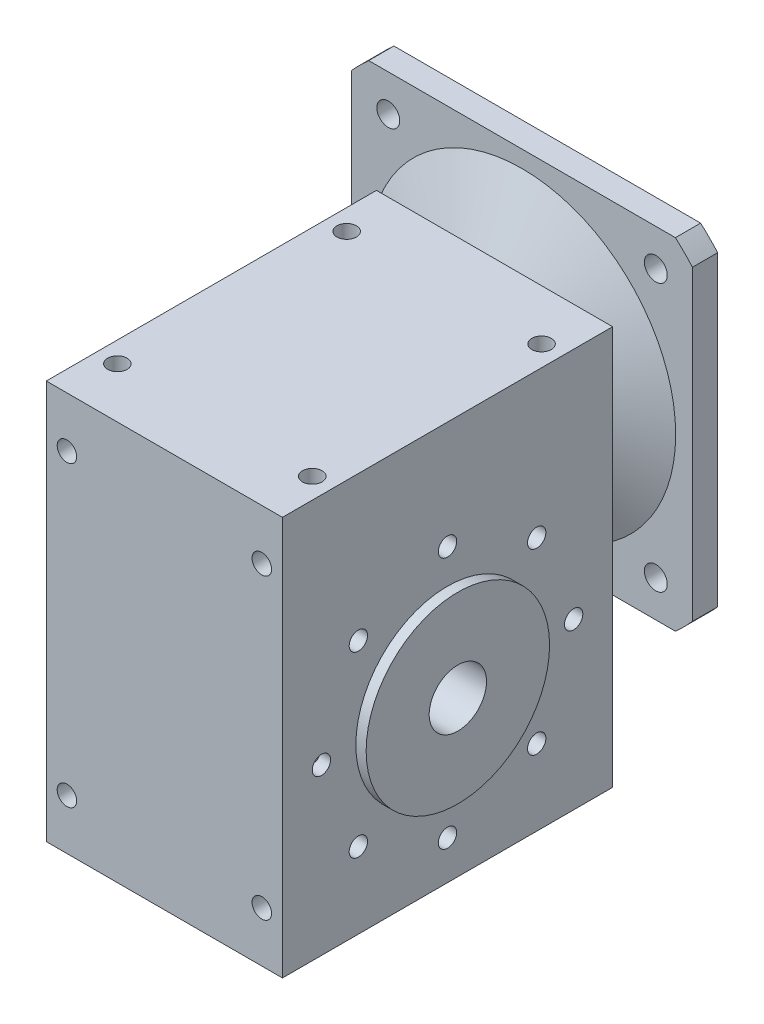
SolidWorks part; units mm, degrees
material "1060 Сплав"
ref_plane "Спереди" through (0, 0, 0) normal (0, 0, 1) x (1, 0, 0)
ref_plane "Сверху" through (0, 0, 0) normal (0, 1, 0) x (1, 0, 0)
ref_plane "Справа" through (0, 0, 0) normal (1, 0, 0) x (0, 0, -1)
sketch "Эскиз1" plane through (0, 0, 0) normal (0, 1, 0) x (1, 0, 0)
  line L0 (0, 0) -> (0, 72) construction
  line L1 (-51.5, 72) -> (51.5, 72)
  line L2 (-51.5, 72) -> (-51.5, -72)
  line L3 (-51.5, -72) -> (51.5, -72)
  line L4 (51.5, 72) -> (51.5, -72)
  line L5 (0, 0) -> (51.5, 0) construction
  point P7 (51.5, 0)
  point P10 (0, 72)
  dimension "D1" = 103
  dimension "D2" = 144
extrude "Бобышка-Вытянуть1" add sketch "Эскиз1" along normal blind 174
sketch "Эскиз2" plane through (0, 0, 72) normal (0, 0, 1) x (1, 0, 0)
  line L0 (-109.3819, 72) -> (115.1187, 72) construction
  line L1 (-51.5, 0) -> (51.5, 0) construction
  dimension "D1" = 72
sketch "Эскиз3" plane through (51.5, 0, 0) normal (1, 0, 0) x (0, 0, -1)
  line L0 (-72, 72) -> (72, 72) construction
  line L1 (-72, 0) -> (72, 0) construction
  line L2 (-72, 174) -> (-72, 0) construction
  line L3 (72, 174) -> (72, 0) construction
  circle A0 centre (0, 72) radius 12.5
  dimension "D2" = 25
  dimension "D1" = 72
extrude "Вырез-Вытянуть1" cut sketch "Эскиз3" against normal through all
sketch "Эскиз4" plane through (51.5, 0, 0) normal (1, 0, 0) x (0, 0, -1)
  line L0 (0, 72) -> (0, 127) construction
  circle A1 centre (0, 127) radius 4
  circle A2 centre (38.8909, 110.8909) radius 4
  circle A3 centre (55, 72) radius 4
  circle A4 centre (38.8909, 33.1091) radius 4
  circle A5 centre (0, 17) radius 4
  circle A6 centre (-38.8909, 33.1091) radius 4
  circle A7 centre (-55, 72) radius 4
  circle A8 centre (-38.8909, 110.8909) radius 4
  point P22 (0, 72)
  dimension "D2" = 8
  dimension "D1" = 55
  dimension "D3" = 8
extrude "Вырез-Вытянуть2" cut sketch "Эскиз4" against normal through all
sketch "Эскиз5" plane through (0, 174, 0) normal (0, 1, 0) x (1, 0, 0)
  line L0 (0, 72) -> (0, -65.0127) construction
  line L1 (-42.5, 50) -> (42.5, 50) construction
  line L2 (-42.5, 50) -> (-42.5, -50) construction
  line L3 (-42.5, -50) -> (42.5, -50) construction
  line L4 (42.5, 50) -> (42.5, -50) construction
  line L5 (51.5, 72) -> (-51.5, 72) construction
  line L6 (-51.5, 0) -> (51.5, 0) construction
  line L7 (-51.5, 72) -> (-51.5, -72) construction
  line L8 (51.5, -72) -> (51.5, 72) construction
  circle A0 centre (-42.5, 50) radius 4.25
  circle A1 centre (42.5, 50) radius 4.25
  circle A2 centre (42.5, -50) radius 4.25
  circle A3 centre (-42.5, -50) radius 4.25
  point P15 (-42.5, 0)
  point P16 (0, -50)
  dimension "D3" = 8.5
  dimension "D1" = 85
  dimension "D2" = 100
extrude "Вырез-Вытянуть3" cut sketch "Эскиз5" against normal through all
ref_plane "Плоскость1" through (0, 0, 0) normal (1, 0, 0) x (0, 0, -1)
sketch "Эскиз6" plane through (0, 0, 0) normal (1, 0, 0) x (0, 0, -1)
  line L0 (89, 146) -> (72, 146)
  line L1 (72, 146) -> (72, 174)
  line L2 (72, 174) -> (84, 202)
  line L3 (84, 202) -> (84, 235)
  line L4 (84, 235) -> (95, 235)
  line L5 (95, 235) -> (95, 200)
  line L6 (95, 200) -> (89, 200)
  line L8 (79, 152.5) -> (89, 152.5)
  line L9 (89, 152.5) -> (89, 146)
  line L10 (-119.058, 135) -> (159.0244, 135) construction
  line L11 (-72, 0) -> (72, 0) construction
  line L12 (-72, 174) -> (72, 174) construction
  line L13 (72, 174) -> (72, 0) construction
  line L14 (79, 152.5) -> (79, 176.6667)
  line L15 (79, 176.6667) -> (89, 200)
  point P16 (0, 174)
  dimension "D1" = 135
  dimension "D2" = 95
  dimension "D3" = 200
  dimension "D4" = 130
  dimension "D5" = 22
  dimension "D6" = 10
  dimension "D8" = 11
  dimension "D9" = 35
  dimension "D10" = 33
  dimension "D7" = 6
  dimension "D11" = 6
  dimension "D12" = 6
revolve "Повернуть1" add sketch "Эскиз6" angle 360 about L10
sketch "Эскиз7" plane through (0, 0, 0) normal (0, -1, 0) x (1, 0, 0)
  line L1 (-35, -70) -> (35, -70)
  line L2 (-35, -70) -> (-35, 70)
  line L3 (-35, 70) -> (35, 70)
  line L4 (35, -70) -> (35, 70)
  line L5 (-35, -70) -> (35, 70) construction
  line L6 (-35, 70) -> (35, -70) construction
  point P0 (0, 0)
  dimension "D1" = 70
  dimension "D2" = 140
extrude "Вырез-Вытянуть4" cut sketch "Эскиз7" against normal blind 169
sketch "Эскиз8" plane through (0, 0, 0) normal (1, 0, 0) x (0, 0, -1)
  circle A0 centre (0, 72) radius 40
  circle A1 centre (0, 72) radius 12.5
  dimension "D1" = 80
extrude "Бобышка-Вытянуть2" add sketch "Эскиз8" along normal mid plane 112
sketch "Эскиз9" plane through (0, 0, 72) normal (0, 0, 1) x (1, 0, 0)
  line L0 (-42.5, 152) -> (42.5, 152) construction
  line L1 (-42.5, 22) -> (-42.5, 152) construction
  line L2 (51.5, 174) -> (51.5, 0) construction
  line L3 (-51.5, 174) -> (51.5, 174) construction
  line L4 (-51.5, 0) -> (51.5, 0) construction
  circle A0 centre (-42.5, 152) radius 4.25
  circle A1 centre (42.5, 152) radius 4.25
  circle A2 centre (42.5, 22) radius 4.25
  circle A3 centre (-42.5, 22) radius 4.25
  point P8 (0, 152)
  point P11 (51.5, 87)
  point P12 (-42.5, 87)
  dimension "D1" = 85
  dimension "D3" = 8.5
  dimension "D2" = 130
  dimension "D4" = 22
  dimension "D5" = 22
extrude "Вырез-Вытянуть5" cut sketch "Эскиз9" against normal up to surface (144 mm away) up to face at (6.5, 109.5, -72)
sketch "Эскиз10" plane through (0, 0, -95) normal (0, 0, -1) x (-1, 0, 0)
  line L0 (-58.3363, 193.3363) -> (0, 135) construction
  line L1 (0, 135) -> (0, 0) construction
  circle A0 centre (-58.3363, 193.3363) radius 5
  circle A1 centre (58.3363, 193.3363) radius 5
  circle A2 centre (58.3363, 76.6637) radius 5
  circle A3 centre (-58.3363, 76.6637) radius 5
  point P15 (0, 135)
  dimension "D1" = 45
  dimension "D3" = 10
  dimension "D2" = 82.5
  dimension "D4" = 4
extrude "Вырез-Вытянуть6" cut sketch "Эскиз10" against normal blind 17
sketch "Эскиз11" plane through (0, 0, -95) normal (0, 0, -1) x (-1, 0, 0)
  line L1 (74.3363, 209.3363) -> (-74.3363, 209.3363)
  line L2 (74.3363, 209.3363) -> (74.3363, 60.6637)
  line L3 (74.3363, 60.6637) -> (-74.3363, 60.6637)
  line L4 (-74.3363, 209.3363) -> (-74.3363, 60.6637)
  line L5 (74.3363, 209.3363) -> (-74.3363, 60.6637) construction
  line L6 (74.3363, 60.6637) -> (-74.3363, 209.3363) construction
  circle A4 centre (58.3363, 193.3363) radius 5 construction
  circle A8 centre (58.3363, 76.6637) radius 5 construction
  point P0 (0, 135)
  dimension "D1" = 11
  dimension "D2" = 11
  dimension "D3" = 11
extrude "Вырез-Вытянуть7" cut sketch "Эскиз11" against normal blind 17 flip side to cut
equation "\"D1@Эскиз6\"=72+63"
